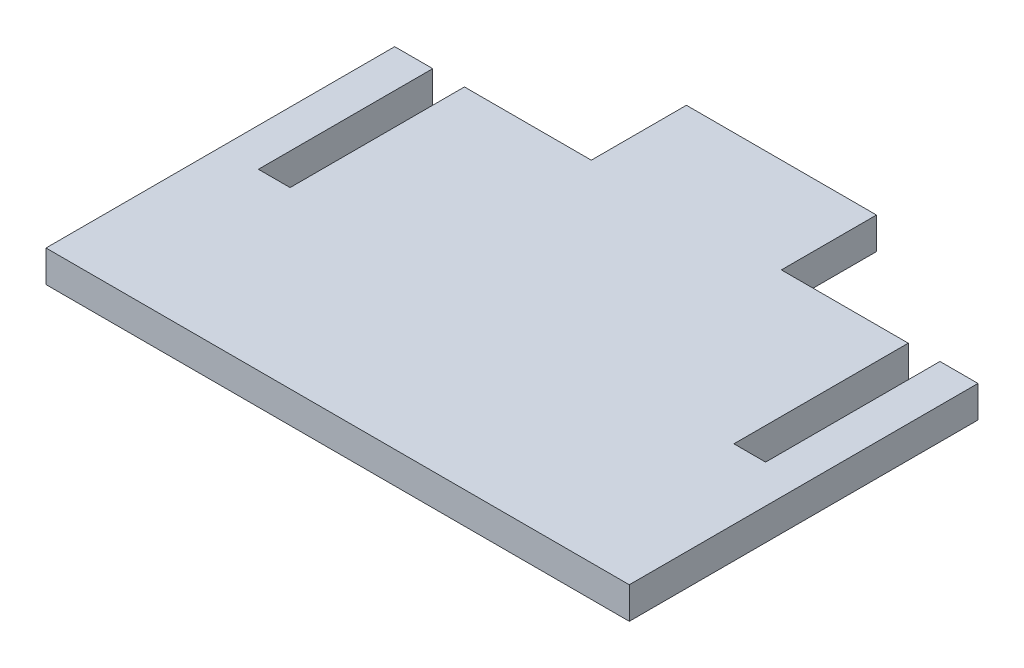
SolidWorks part; units mm, degrees
ref_plane "Front Plane" through (0, 0, 0) normal (0, 0, 1) x (1, 0, 0)
ref_plane "Top Plane" through (0, 0, 0) normal (0, 1, 0) x (1, 0, 0)
ref_plane "Right Plane" through (0, 0, 0) normal (1, 0, 0) x (0, 0, -1)
sketch "Sketch1" plane through (0, 0, 0) normal (0, 1, 0) x (1, 0, 0)
  line L1 (-46, 27.5) -> (46, 27.5)
  line L2 (-46, 27.5) -> (-46, -27.5)
  line L3 (-46, -27.5) -> (46, -27.5)
  line L4 (46, 27.5) -> (46, -27.5)
  line L5 (-46, 27.5) -> (46, -27.5) construction
  line L6 (-46, -27.5) -> (46, 27.5) construction
  point P0 (0, 0)
  dimension "D1" = 92
  dimension "D2" = 55
extrude "Boss-Extrude1" add sketch "Sketch1" along normal mid plane 5
sketch "Sketch2" plane through (0, 2.5, 0) normal (0, 1, 0) x (1, 0, 0)
  line L0 (46, 27.5) -> (-46, 27.5) construction
  line L1 (-40, 27.5) -> (-35, 27.5)
  line L2 (-40, 27.5) -> (-40, 0)
  line L3 (-40, 0) -> (-35, 0)
  line L4 (-35, 27.5) -> (-35, 0)
  line L5 (-46, 27.5) -> (-46, -27.5) construction
  line L6 (46, -27.5) -> (46, 27.5) construction
  line L7 (35, 27.5) -> (40, 27.5)
  line L8 (35, 27.5) -> (35, 0)
  line L9 (35, 0) -> (40, 0)
  line L10 (40, 27.5) -> (40, 0)
  dimension "D1" = 6
  dimension "D2" = 5
  dimension "D3" = 27.5
  dimension "D4" = 5
  dimension "D5" = 6
extrude "Cut-Extrude1" cut sketch "Sketch2" against normal through all
sketch "Sketch3" plane through (0, 2.5, 0) normal (0, 1, 0) x (1, 0, 0)
  line L0 (35, 27.5) -> (-35, 27.5) construction
  line L1 (-14.99, 42.5) -> (14.99, 42.5)
  line L2 (-14.99, 42.5) -> (-14.99, 27.5)
  line L3 (-14.99, 27.5) -> (14.99, 27.5)
  line L4 (14.99, 42.5) -> (14.99, 27.5)
  line L5 (-14.99, 42.5) -> (14.99, 27.5) construction
  line L6 (-14.99, 27.5) -> (14.99, 42.5) construction
  point P0 (0, 35)
  dimension "D1" = 15
  dimension "D2" = 29.98
  dimension "D3" = 0
extrude "Boss-Extrude2" add sketch "Sketch3" against normal blind 5
